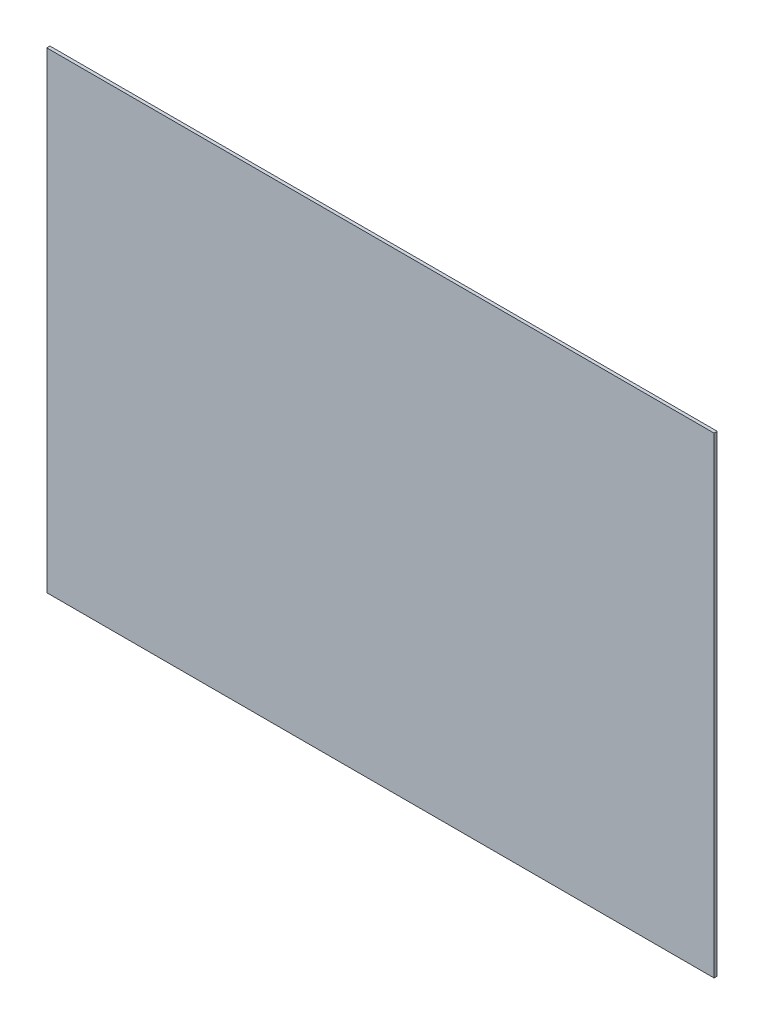
SolidWorks part; units mm, degrees
ref_plane "Front Plane" through (0, 0, 0) normal (0, 0, 1) x (1, 0, 0)
ref_plane "Top Plane" through (0, 0, 0) normal (0, 1, 0) x (1, 0, 0)
ref_plane "Right Plane" through (0, 0, 0) normal (1, 0, 0) x (0, 0, -1)
sketch "Sketch1" plane through (0, 0, 0) normal (0, 0, 1) x (1, 0, 0)
  line L1 (0, 0) -> (420, 0)
  line L2 (0, 0) -> (0, 297)
  line L3 (0, 297) -> (420, 297)
  line L4 (420, 0) -> (420, 297)
  dimension "D1" = 297
  dimension "D2" = 420
extrude "Boss-Extrude1" add sketch "Sketch1" along normal blind 2
